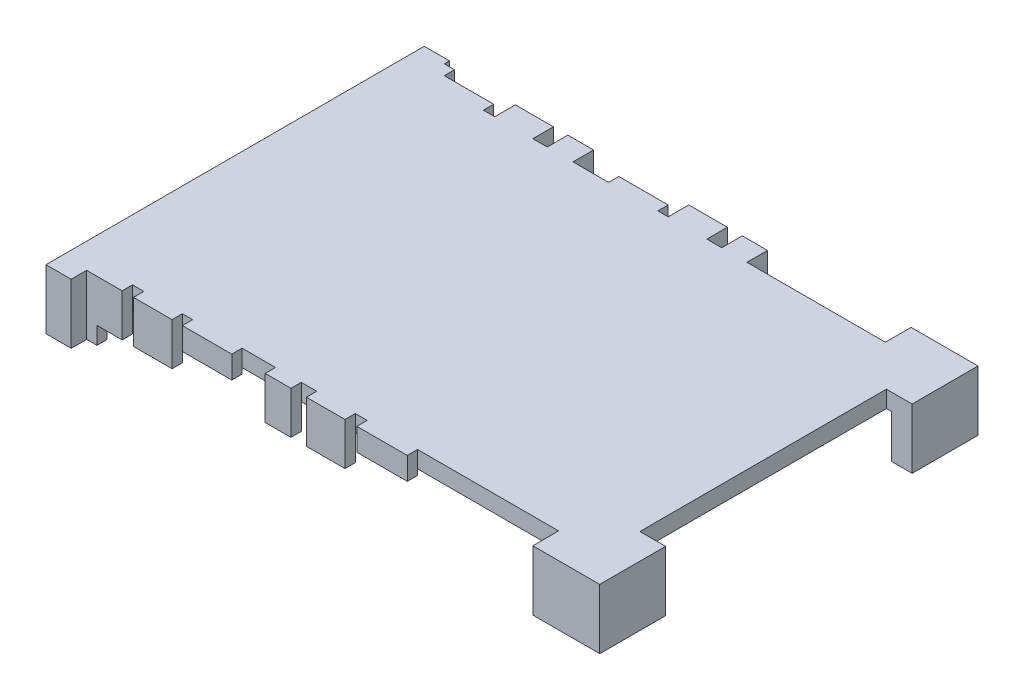
SolidWorks part; units mm, degrees
ref_plane "Front Plane" through (0, 0, 0) normal (0, 0, 1) x (1, 0, 0)
ref_plane "Top Plane" through (0, 0, 0) normal (0, 1, 0) x (1, 0, 0)
ref_plane "Right Plane" through (0, 0, 0) normal (1, 0, 0) x (0, 0, -1)
sketch "Sketch1" plane through (0, 0, 0) normal (0, 1, 0) x (1, 0, 0)
  line L0 (0, -31.75) -> (102.6, -31.75) construction
  line L1 (0, 0) -> (102.6, 0)
  line L2 (0, 0) -> (0, -63.5)
  line L3 (0, -63.5) -> (102.6, -63.5)
  line L4 (102.6, 0) -> (102.6, -63.5)
  line L5 (94.6, -63.5) -> (94.6, -68.5)
  line L6 (94.6, -68.5) -> (107.6, -68.5)
  line L7 (107.6, -68.5) -> (107.6, -55.7)
  line L8 (107.6, -55.7) -> (102.6, -55.7)
  line L9 (102.6, -55.7) -> (102.6, -63.5)
  line L10 (94.6, 5) -> (107.6, 5)
  line L11 (107.6, 5) -> (107.6, -7.8)
  line L12 (107.6, -7.8) -> (102.6, -7.8)
  line L13 (94.6, 0) -> (94.6, 5)
  dimension "D1" = 107.6
  dimension "D2" = 73.5
  dimension "D3" = 5
  dimension "D4" = 13
  dimension "D5" = 5
  dimension "D6" = 12.8
extrude "Corners" add sketch "Sketch1" against normal blind 8.4 contours L7 L8 L4 L3 L5 L6 | L13 L1 L4 L12 L11 L10
sketch "Sketch2" plane through (0, 0, 0) normal (0, 1, 0) x (1, 0, 0)
  line L1 (102.6, -63.5) -> (0, -63.5)
  line L2 (102.6, -63.5) -> (102.6, 0)
  line L3 (102.6, 0) -> (0, 0)
  line L4 (0, -63.5) -> (0, 0)
extrude "Master" add sketch "Sketch2" along normal blind 3 separate body
sketch "Sketch3" plane through (0, 0, 0) normal (0, -1, 0) x (1, 0, 0)
  line L0 (0, 0) -> (0, 63.5) construction
  line L1 (0, 68.5) -> (4.9, 68.5)
  line L2 (0, 68.5) -> (0, -5)
  line L3 (0, -5) -> (4.9, -5)
  line L4 (4.9, 68.5) -> (4.9, -5)
  line L5 (0, 63.5) -> (102.6, 63.5) construction
  dimension "D1" = 73.5
  dimension "D2" = 5
  dimension "D3" = 4.9
extrude "End Tab" add sketch "Sketch3" along normal blind 8.36 and the other way blind 3.27
sketch "Sketch4" plane through (0, -8.36, 0) normal (0, -1, 0) x (1, 0, 0)
  line L0 (0, 31.75) -> (102.6, 31.75) construction
  line L1 (0, 68.5) -> (0, -5) construction
  line L2 (102.6, 63.5) -> (102.6, 0) construction
  line L3 (1.4, 15.4) -> (4.6, 15.4)
  line L4 (1.4, 54.5) -> (4.6, 54.5)
  line L5 (1.4, 54.5) -> (1.4, 48.1)
  line L6 (1.4, 48.1) -> (4.6, 48.1)
  line L7 (4.6, 54.5) -> (4.6, 48.1)
  line L8 (4.6, 9) -> (4.6, 15.4)
  line L9 (1.4, 9) -> (4.6, 9)
  line L10 (1.4, 9) -> (1.4, 15.4)
  line L12 (4.9, 68.5) -> (0, 68.5) construction
  dimension "D1" = 6.4
  dimension "D2" = 14
  dimension "D3" = 3.2
  dimension "D4" = 4.6
extrude "Male Connectors" add sketch "Sketch4" along normal blind 1.65
sketch "Sketch5" plane through (0, 0, 0) normal (0, -1, 0) x (1, 0, 0)
  line L0 (102.6, 0) -> (4.9, 0) construction
  line L1 (6.9, 0) -> (16.5, 0)
  line L2 (6.9, 0) -> (6.9, -2)
  line L3 (6.9, -2) -> (16.5, -2)
  line L4 (16.5, 0) -> (16.5, -2)
  line L5 (4.9, -5) -> (4.9, 68.5) construction
  line L7 (18.7, 0) -> (26.1, 0)
  line L8 (18.7, 0) -> (18.7, -4)
  line L9 (18.7, -4) -> (26.1, -4)
  line L10 (26.1, 0) -> (26.1, -4)
  line L11 (28.9, 0) -> (33.9, 0)
  line L12 (28.9, 0) -> (28.9, -4)
  line L13 (28.9, -4) -> (33.9, -4)
  line L14 (33.9, 0) -> (33.9, -4)
  line L15 (40.8, 0) -> (50.4, 0)
  line L16 (40.8, 0) -> (40.8, -2)
  line L17 (40.8, -2) -> (50.4, -2)
  line L18 (50.4, 0) -> (50.4, -2)
  line L19 (52.4, 0) -> (59.9, 0)
  line L20 (52.4, 0) -> (52.4, -4)
  line L21 (52.4, -4) -> (59.9, -4)
  line L22 (59.9, 0) -> (59.9, -4)
  line L23 (62.8, 0) -> (67.7, 0)
  line L24 (62.8, 0) -> (62.8, -4)
  line L25 (62.8, -4) -> (67.7, -4)
  line L26 (67.7, 0) -> (67.7, -4)
  line L28 (94.6, 0) -> (94.6, -5) construction
  dimension "D1" = 2
  dimension "D2" = 26.9
  dimension "D3" = 2
  dimension "D4" = 7.4
  dimension "D5" = 2.2
  dimension "D6" = 4
  dimension "D7" = 5
  dimension "D8" = 4
  dimension "D9" = 2.8
  dimension "D10" = 9.6
  dimension "D11" = 6.9
  dimension "D12" = 2
  dimension "D13" = 2
  dimension "D14" = 7.5
  dimension "D15" = 4
  dimension "D16" = 4
  dimension "D17" = 4.9
  dimension "D18" = 2.9
extrude "Right Terminals" add sketch "Sketch5" along normal blind 5 and the other way up to surface (3.27 mm away) other way up to face at (2.45, 3.27, 31.75)
sketch "Sketch7" plane through (0, 0, 0) normal (0, -1, 0) x (1, 0, 0)
  line L0 (4.9, 63.5) -> (102.6, 63.5) construction
  line L1 (6.9, 63.5) -> (11.8, 63.5)
  line L2 (6.9, 63.5) -> (6.9, 65.5)
  line L3 (6.9, 65.5) -> (11.8, 65.5)
  line L4 (11.8, 63.5) -> (11.8, 65.5)
  line L5 (4.9, -5) -> (4.9, 68.5) construction
  line L6 (14, 63.5) -> (21.5, 63.5)
  line L7 (14, 63.5) -> (14, 65.5)
  line L8 (14, 65.5) -> (21.5, 65.5)
  line L9 (21.5, 63.5) -> (21.5, 65.5)
  line L10 (23.5, 63.5) -> (33.1, 63.5)
  line L11 (23.5, 63.5) -> (23.5, 65.5)
  line L12 (23.5, 65.5) -> (33.1, 65.5)
  line L13 (33.1, 63.5) -> (33.1, 65.5)
  line L14 (39.6, 63.5) -> (44.6, 63.5)
  line L15 (39.6, 63.5) -> (39.6, 65.5)
  line L16 (39.6, 65.5) -> (44.6, 65.5)
  line L17 (44.6, 63.5) -> (44.6, 65.5)
  line L18 (47.6, 63.5) -> (55.1, 63.5)
  line L19 (47.6, 63.5) -> (47.6, 65.5)
  line L20 (47.6, 65.5) -> (55.1, 65.5)
  line L21 (55.1, 63.5) -> (55.1, 65.5)
  line L22 (57.4, 63.5) -> (67.2, 63.5)
  line L23 (57.4, 63.5) -> (57.4, 65.5)
  line L24 (57.4, 65.5) -> (67.2, 65.5)
  line L25 (67.2, 63.5) -> (67.2, 65.5)
  line L28 (94.6, 63.5) -> (94.6, 68.5) construction
  point P28 (44.6, 64.5)
  dimension "D1" = 2
  dimension "D2" = 27.4
  dimension "D3" = 2
  dimension "D4" = 2.2
  dimension "D5" = 7.5
  dimension "D6" = 2
  dimension "D7" = 2
  dimension "D8" = 2
  dimension "D9" = 2
  dimension "D10" = 2
  dimension "D11" = 2
  dimension "D12" = 9.6
  dimension "D13" = 6.5
  dimension "D14" = 5
  dimension "D15" = 3
  dimension "D16" = 7.5
  dimension "D17" = 2.3
  dimension "D18" = 9.8
extrude "Left Terminals" add sketch "Sketch7" along normal blind 5 and the other way up to surface (3.27 mm away) separate body other way up to face at (2.45, 3.27, 31.75)
sketch "Sketch8" plane through (0, -5, 0) normal (0, -1, 0) x (1, 0, 0)
  line L0 (16.5, 0) -> (6.9, 0) construction
  line L1 (6.9, -2) -> (16.5, -2)
  line L2 (6.9, -2) -> (6.9, 0)
  line L3 (6.9, 0) -> (16.5, 0)
  line L4 (16.5, -2) -> (16.5, 0)
  line L5 (16.5, -2) -> (16.5, 0) construction
  line L7 (40.8, -2) -> (50.4, -2)
  line L8 (40.8, -2) -> (40.8, 0)
  line L9 (40.8, 0) -> (50.4, 0)
  line L10 (50.4, -2) -> (50.4, 0)
extrude "Gold Plate Adjustments (Right)" cut sketch "Sketch8" against normal blind 3.9
sketch "Sketch9" plane through (0, -5, 0) normal (0, -1, 0) x (1, 0, 0)
  line L1 (23.5, 63.5) -> (33.1, 63.5)
  line L2 (23.5, 63.5) -> (23.5, 65.5)
  line L3 (23.5, 65.5) -> (33.1, 65.5)
  line L4 (33.1, 63.5) -> (33.1, 65.5)
  line L5 (57.4, 63.5) -> (67.2, 63.5)
  line L6 (57.4, 63.5) -> (57.4, 65.5)
  line L7 (57.4, 65.5) -> (67.2, 65.5)
  line L8 (67.2, 63.5) -> (67.2, 65.5)
extrude "Gold Plate Adjustments (Left)" cut sketch "Sketch9" against normal blind 3.9
sketch "Sketch10" plane through (0, 0, 0) normal (0, 1, 0) x (1, 0, 0)
  line L0 (102.6, -7.8) -> (107.6, -7.8)
  line L1 (107.6, -7.8) -> (107.6, 5)
  line L2 (107.6, 5) -> (94.6, 5)
  line L3 (94.6, 5) -> (94.6, 0)
  line L4 (94.6, 0) -> (102.6, 0)
  line L5 (102.6, 0) -> (102.6, -7.8)
  line L6 (102.6, -55.7) -> (107.6, -55.7)
  line L7 (107.6, -55.7) -> (107.6, -68.5)
  line L8 (107.6, -68.5) -> (94.6, -68.5)
  line L9 (94.6, -68.5) -> (94.6, -63.5)
  line L10 (94.6, -63.5) -> (94.6, -68.5) construction
  line L11 (94.6, -63.5) -> (102.6, -63.5)
  line L12 (102.6, -63.5) -> (102.6, -55.7)
extrude "Corner Adjustment" add sketch "Sketch10" along normal blind 3
sketch "Sketch11" plane through (0, 3, 0) normal (0, 1, 0) x (1, 0, 0)
sketch "Sketch13" plane through (0, 3, 0) normal (0, 1, 0) x (1, 0, 0)
  line L0 (102.6, -55.7) -> (102.6, -7.8) construction
  line L1 (4.9, 0) -> (102.6, 0)
  line L2 (4.9, 0) -> (4.9, -63.5)
  line L3 (4.9, -63.5) -> (102.6, -63.5)
  line L4 (102.6, 0) -> (102.6, -63.5)
  line L5 (4.9, -63.5) -> (94.6, -63.5) construction
extrude "Boss-Extrude1" add sketch "Sketch13" along normal up to surface (0.27 mm away) up to face at (2.45, 3.27, 31.75)
sketch "Sketch14" plane through (0, 3, 0) normal (0, 1, 0) x (1, 0, 0)
  line L1 (94.6, -68.5) -> (107.6, -68.5)
  line L2 (94.6, -68.5) -> (94.6, -55.7)
  line L3 (94.6, -55.7) -> (107.6, -55.7)
  line L4 (107.6, -68.5) -> (107.6, -55.7)
  line L5 (107.6, -7.8) -> (94.6, -7.8)
  line L6 (107.6, -7.8) -> (107.6, 5)
  line L7 (107.6, 5) -> (94.6, 5)
  line L8 (94.6, -7.8) -> (94.6, 5)
extrude "Boss-Extrude2" add sketch "Sketch14" along normal up to surface (0.27 mm away) up to face at (35.7036, 3.27, 31.4643)
sketch "Sketch15" plane through (0, 3.27, 0) normal (0, 1, 0) x (1, 0, 0)
  line L1 (4.9, 0) -> (6.9, 0)
  line L2 (4.9, 0) -> (4.9, 4)
  line L3 (4.9, 4) -> (6.9, 4)
  line L4 (6.9, 0) -> (6.9, 4)
  line L5 (4.9, -63.5) -> (6.9, -63.5)
  line L6 (4.9, -63.5) -> (4.9, -65.5)
  line L7 (4.9, -65.5) -> (6.9, -65.5)
  line L8 (6.9, -63.5) -> (6.9, -65.5)
  dimension "D1" = 4
  dimension "D2" = 2
sketch "Sketch17" plane through (0, -5, 0) normal (0, -1, 0) x (1, 0, 0)
  line L1 (18.7, 0) -> (26.1, 0)
  line L2 (18.7, 0) -> (18.7, -2)
  line L3 (18.7, -2) -> (26.1, -2)
  line L4 (26.1, 0) -> (26.1, -2)
  line L5 (26.1, -4) -> (26.1, 0) construction
  line L6 (33.9, -4) -> (33.9, 0) construction
  line L7 (28.9, 0) -> (33.9, 0)
  line L8 (28.9, 0) -> (28.9, -2)
  line L9 (28.9, -2) -> (33.9, -2)
  line L10 (33.9, 0) -> (33.9, -2)
  line L11 (59.9, -4) -> (59.9, 0) construction
  line L12 (52.4, 0) -> (59.9, 0)
  line L13 (52.4, 0) -> (52.4, -2)
  line L14 (52.4, -2) -> (59.9, -2)
  line L15 (59.9, 0) -> (59.9, -2)
  line L16 (62.8, 0) -> (62.8, -4) construction
  line L17 (67.7, 0) -> (62.8, 0)
  line L18 (67.7, 0) -> (67.7, -2)
  line L19 (67.7, -2) -> (62.8, -2)
  line L20 (62.8, 0) -> (62.8, -2)
  dimension "D1" = 2
  dimension "D2" = 2
extrude "Cut-Extrude2" cut sketch "Sketch17" against normal up to surface (5 mm away) up to face at (46.7719, 0, 31.75)
sketch "Sketch19" plane through (0, 0, -4) normal (0, 0, -1) x (-1, 0, 0)
  line L0 (-33.9, 3.27) -> (-33.9, -5) construction
  line L1 (-18.7, -5) -> (-33.9, -5)
  line L2 (-18.7, -5) -> (-18.7, -4.6)
  line L3 (-18.7, -4.6) -> (-33.9, -4.6)
  line L4 (-33.9, -5) -> (-33.9, -4.6)
  dimension "D1" = 0.4
extrude "Cut-Extrude4" cut sketch "Sketch19" against normal blind 0.75
sketch "Sketch20" plane through (0, 0, -4) normal (0, 0, -1) x (-1, 0, 0)
  line L0 (-52.4, 3.27) -> (-52.4, -5) construction
  line L2 (-67.7, -5) -> (-67.7, 0)
  line L4 (-52.4, -5) -> (-52.4, 0)
  line L5 (-62.8, -5) -> (-67.7, -5)
  line L6 (-67.7, 0) -> (-62.8, 0)
  line L7 (-62.8, 3.27) -> (-62.8, -5) construction
  line L8 (-62.8, 0) -> (-62.8, -5)
  line L9 (-59.9, -5) -> (-52.4, -5)
  line L10 (-52.4, 0) -> (-59.9, 0)
  line L11 (-59.9, 3.27) -> (-59.9, -5) construction
  line L12 (-59.9, 0) -> (-59.9, -5)
extrude "Boss-Extrude5" add sketch "Sketch20" against normal blind 2.165
extrude "Boss-Extrude3" add sketch "Sketch15" against normal up to surface (11.63 mm away) up to face at (2.45, -8.36, 31.75)
sketch "Sketch21" plane through (0, 0, -4) normal (0, 0, -1) x (-1, 0, 0)
  line L0 (-52.4, 3.27) -> (-52.4, -5) construction
  line L1 (-67.7, -5) -> (-52.4, -5)
  line L2 (-67.7, -5) -> (-67.7, -4.6)
  line L3 (-67.7, -4.6) -> (-52.4, -4.6)
  line L4 (-52.4, -5) -> (-52.4, -4.6)
  dimension "D1" = 0.4
extrude "Cut-Extrude5" cut sketch "Sketch21" against normal blind 1.65
sketch "Sketch22" plane through (0, -8.36, 0) normal (0, -1, 0) x (1, 0, 0)
  line L1 (6.9, 0) -> (4.9, 0)
  line L2 (6.9, 0) -> (6.9, -3.0747)
  line L3 (6.9, -3.0747) -> (4.9, -3.0747)
  line L4 (4.9, 0) -> (4.9, -3.0747)
  line L5 (6.9, 0) -> (6.9, -4) construction
  point P5 (6.9, -1.6696)
  point P8 (0, 0)
extrude "Cut-Extrude7" cut sketch "Sketch22" against normal up to surface (8.36 mm away) up to face at (48.2447, 0, 24.6621)
sketch "Sketch23" plane through (0, -8.4, 0) normal (0, -1, 0) x (1, 0, 0)
  line L0 (94.6, 0) -> (94.6, -5) construction
  line L1 (94.6, -1) -> (103.6, -1)
  line L2 (94.6, -1) -> (94.6, 7.8)
  line L3 (94.6, 7.8) -> (103.6, 7.8)
  line L4 (103.6, -1) -> (103.6, 7.8)
  line L5 (107.6, 7.8) -> (102.6, 7.8) construction
  line L6 (102.6, 0) -> (102.6, 7.8) construction
  line L7 (94.6, 0) -> (102.6, 0) construction
  dimension "D1" = 1
  dimension "D2" = 1
extrude "Cut-Extrude8" cut sketch "Sketch23" against normal up to surface (8.4 mm away) up to face at (45.2195, 0, 22.6588)
